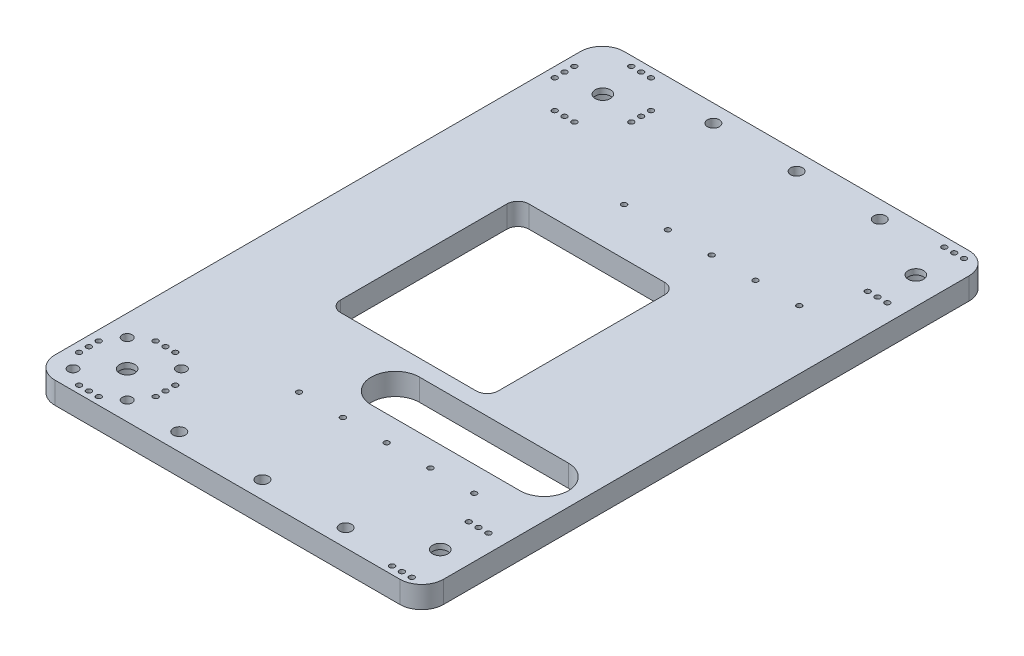
SolidWorks part; units mm, degrees
ref_plane "Front Plane" through (0, 0, 0) normal (0, 0, 1) x (1, 0, 0)
ref_plane "Top Plane" through (0, 0, 0) normal (0, 1, 0) x (1, 0, 0)
ref_plane "Right Plane" through (0, 0, 0) normal (1, 0, 0) x (0, 0, -1)
sketch "Sketch1" plane through (0, 0, 0) normal (0, 1, 0) x (1, 0, 0)
  line L0 (0, 134.94) -> (165, 134.94) construction
  line L1 (10, 0) -> (167.5, 0)
  line L2 (0, 10) -> (0, 250)
  line L3 (10, 260) -> (167.5, 260)
  line L4 (177.5, 10) -> (177.5, 250)
  line L7 (48.5, 91.94) -> (110.5, 91.94)
  line L8 (43.5, 96.94) -> (43.5, 172.94)
  line L9 (48.5, 177.94) -> (110.5, 177.94)
  line L10 (115.5, 96.94) -> (115.5, 172.94)
  line L11 (43.5, 91.94) -> (115.5, 177.94) construction
  line L12 (43.5, 177.94) -> (115.5, 91.94) construction
  arc A0 (0, 10) -> (10, 0) centre (10, 10) ccw
  arc A1 (167.5, 0) -> (177.5, 10) centre (167.5, 10) ccw
  arc A2 (177.5, 250) -> (167.5, 260) centre (167.5, 250) ccw
  arc A3 (10, 260) -> (0, 250) centre (10, 250) ccw
  arc A7 (110.5, 177.94) -> (115.5, 172.94) centre (110.5, 172.94) cw
  arc A8 (115.5, 96.94) -> (110.5, 91.94) centre (110.5, 96.94) cw
  arc A9 (48.5, 91.94) -> (43.5, 96.94) centre (48.5, 96.94) cw
  arc A11 (43.5, 172.94) -> (48.5, 177.94) centre (48.5, 172.94) cw
  point P7 (0, 0)
  point P10 (177.5, 0)
  point P15 (0, 260)
  point P20 (35, 60)
  point P21 (35, 190)
  point P28 (79.5, 134.94)
  point P29 (15.4848, 130)
  point P31 (135.4848, 130)
  point P44 (15.4848, 120)
  point P45 (135.4848, 120)
  dimension "D3" = 10
  dimension "D5" = 79.5
  dimension "D8" = 5
  dimension "D1" = 177.5
  dimension "D2" = 260
  dimension "D4" = 125.06
  dimension "D6" = 86
  dimension "D7" = 72
extrude "Boss-Extrude1" add sketch "Sketch1" along normal blind 10
sketch "Sketch3" plane through (0, 10, 0) normal (0, 1, 0) x (1, 0, 0)
  line L0 (92, 73.46) -> (160, 73.46) construction
  line L1 (92, 84.46) -> (92, 62.46) construction
  line L2 (92, 84.46) -> (160, 84.46)
  line L3 (160, 84.46) -> (160, 62.46) construction
  line L4 (43.5, 134.94) -> (115.5, 134.94) construction
  line L5 (92, 62.46) -> (160, 62.46)
  line L6 (43.5, 172.94) -> (43.5, 96.94) construction
  line L7 (115.5, 96.94) -> (115.5, 172.94) construction
  line L8 (177.5, 10) -> (177.5, 250) construction
  arc A0 (92, 84.46) -> (92, 62.46) centre (92, 73.46) ccw
  arc A1 (160, 62.46) -> (160, 84.46) centre (160, 73.46) ccw
  dimension "D2" = 17.5
  dimension "D4" = 68
  dimension "D1" = 61.48
  dimension "D3" = 22
extrude "Cut-Extrude2" cut sketch "Sketch3" against normal through all
sketch "Sketch5" plane through (0, 0, 0) normal (0, 1, 0) x (1, 0, 0)
  line L0 (0, 250) -> (0, 10) construction
  line L1 (10, 0) -> (167.5, 0) construction
  line L3 (22, 20.97) -> (165, 20.97) construction
  line L5 (22, 20.97) -> (22, 238.23) construction
  line L6 (22, 238.23) -> (165, 238.23) construction
  line L7 (165, 20.97) -> (165, 238.23) construction
  line L9 (177.5, 10) -> (177.5, 250) construction
  circle A0 centre (22, 20.97) radius 9.5
  circle A1 centre (165, 20.97) radius 9.5
  circle A2 centre (165, 238.23) radius 9.5
  circle A3 centre (22, 238.23) radius 9.5
  dimension "D1" = 12.5
  dimension "D2" = 22
  dimension "D5" = 19
  dimension "D4" = 20.97
  dimension "D3" = 217.26
extrude "Cut-Extrude4" cut sketch "Sketch5" along normal blind 6.5
sketch "Sketch7" plane through (0, 6.5, 0) normal (0, 1, 0) x (1, 0, 0)
  circle A0 centre (22, 20.97) radius 8
  circle A1 centre (165, 20.97) radius 8
  circle A2 centre (165, 238.23) radius 8
  circle A3 centre (22, 238.23) radius 8
  dimension "D1" = 16
extrude "Cut-Extrude5" cut sketch "Sketch7" along normal blind 1
sketch "Sketch8" plane through (0, 10, 0) normal (0, 1, 0) x (1, 0, 0)
  line L0 (22, 20.97) -> (165, 20.97) construction
  line L1 (165, 20.97) -> (165, 238.23) construction
  line L2 (93.5, 20.97) -> (93.5, 72.7554) construction
  line L3 (165, 129.6) -> (94.2743, 129.6) construction
  circle A0 centre (22, 20.97) radius 3.5
  circle A1 centre (165, 20.97) radius 3.5
  circle A2 centre (165, 238.23) radius 3.5
  circle A3 centre (22, 238.23) radius 3.5
  dimension "D1" = 7
extrude "Cut-Extrude6" cut sketch "Sketch8" against normal through all
hole_wizard "M4 Clearance Hole1" positions "Sketch11" profile "Sketch10" hole size "M4" standard "ISO" end condition through all
sketch "Sketch11" plane through (0, 10, 0) normal (0, 1, 0) x (-1, 0, 0)
  line L1 (-9.6256, -8.5956) -> (-34.3744, -8.5956) construction
  line L2 (-9.6256, -8.5956) -> (-9.6256, -33.3444) construction
  line L3 (-9.6256, -33.3444) -> (-34.3744, -33.3444) construction
  line L4 (-34.3744, -8.5956) -> (-34.3744, -33.3444) construction
  line L5 (-9.6256, -8.5956) -> (-34.3744, -33.3444) construction
  line L6 (-9.6256, -33.3444) -> (-34.3744, -8.5956) construction
  circle A0 centre (-22, -20.97) radius 17.5 construction
  circle A3 centre (-22, -20.97) radius 3.5 construction
  point P0 (-9.6256, -33.3444)
  point P1 (-34.3744, -33.3444)
  point P3 (-34.3744, -8.5956)
  point P5 (-9.6256, -8.5956)
  dimension "D1" = 35
sketch "Sketch10" plane through (9.6256, 10, -33.3444) normal (1, 0, 0) x (0, 0, 1)
  line L0 (0, 0) -> (0, 10)
  line L1 (0, 10) -> (2.25, 10)
  line L2 (2.25, 10) -> (2.25, 0)
  line L5 (2.25, 0) -> (0, 0)
  line L11 (0, -6.35) -> (0, 107.95) construction
  dimension "Thru Hole Dia." = 4.5
  dimension "Thru Hole Depth" = 10
hole_wizard "M2 Clearance Hole1" positions "Sketch14" profile "Sketch13" hole size "M2" standard "ISO" end condition through all
sketch "Sketch14" plane through (0, 10, 0) normal (0, 1, 0) x (-1, 0, 0)
  line L0 (-177.5, -50.96) -> (-50.3395, -50.96) construction
  line L1 (-177.5, -10) -> (-177.5, -250) construction
  line L8 (-70.5, -199.46) -> (-150.5, -199.46) construction
  line L9 (-115.5, -134.94) -> (-69.9149, -134.94) construction
  line L10 (-115.5, -96.94) -> (-115.5, -172.94) construction
  point P0 (-150.5, -50.96)
  point P17 (-130.5, -50.96)
  point P19 (-110.5, -50.96)
  point P21 (-90.5, -50.96)
  point P23 (-70.5, -50.96)
  point P48 (-70.5, -199.46)
  point P49 (-90.5, -199.46)
  point P50 (-110.5, -199.46)
  point P51 (-130.5, -199.46)
  point P52 (-150.5, -199.46)
  dimension "D1" = 83.98
  dimension "D2" = 27
  dimension "D3" = 20
  dimension "D4" = 20
  dimension "D5" = 20
  dimension "D6" = 20
  dimension "D7" = 64.52
sketch "Sketch13" plane through (150.5, 10, -50.96) normal (1, 0, 0) x (0, 0, 1)
  line L0 (0, 0) -> (0, 10)
  line L1 (0, 10) -> (1.2, 10)
  line L2 (1.2, 10) -> (1.2, 0)
  line L5 (1.2, 0) -> (0, 0)
  line L11 (0, -6.35) -> (0, 107.95) construction
  dimension "Thru Hole Dia." = 2.4
  dimension "Thru Hole Depth" = 10
hole_wizard "M2 Clearance Hole2" positions "Sketch16" profile "Sketch15" hole size "M2" standard "ISO" end condition through all
sketch "Sketch16" plane through (0, 10, 0) normal (0, 1, 0) x (-1, 0, 0)
  line L0 (-177.5, -3.47) -> (-129.2015, -3.47) construction
  line L1 (-177.5, -10) -> (-177.5, -250) construction
  line L3 (-10, 0) -> (-167.5, 0) construction
  line L4 (-165, -20.97) -> (-22, -20.97) construction
  line L6 (-93.5, -20.97) -> (-93.5, -14.0761) construction
  line L8 (-165, -20.97) -> (-165, -238.23) construction
  line L10 (-22, -20.97) -> (-22, -51.973) construction
  line L11 (-4.5, 0) -> (-4.5, -75.94) construction
  line L13 (0, -250) -> (0, -10) construction
  line L14 (-165, -129.6) -> (-68.1928, -129.6) construction
  line L15 (-22, -238.23) -> (-165, -238.23) construction
  line L17 (-22, -238.23) -> (-22, -20.97) construction
  circle A1 centre (-165, -20.97) radius 8 construction
  circle A2 centre (-22, -20.97) radius 3.5 construction
  circle A3 centre (-165, -238.23) radius 8 construction
  circle A4 centre (-22, -238.23) radius 3.5 construction
  point P0 (-165, -3.47)
  point P1 (-169.5, -3.47)
  point P14 (-160.5, -3.47)
  point P21 (-160.5, -38.47)
  point P22 (-169.5, -38.47)
  point P23 (-165, -38.47)
  point P79 (-165, -220.73)
  point P80 (-169.5, -220.73)
  point P81 (-160.5, -220.73)
  point P82 (-160.5, -255.73)
  point P83 (-169.5, -255.73)
  point P84 (-165, -255.73)
  point P87 (-39.5, -242.73)
  point P88 (-39.5, -233.73)
  point P89 (-39.5, -238.23)
  point P99 (-22, -255.73)
  point P100 (-17.5, -255.73)
  point P101 (-26.5, -255.73)
  point P102 (-26.5, -220.73)
  point P103 (-17.5, -220.73)
  point P104 (-22, -220.73)
  point P120 (-4.5, -238.23)
  point P121 (-4.5, -233.73)
  point P122 (-4.5, -242.73)
  dimension "D5" = 17.5
  dimension "D1" = 8
  dimension "D2" = 3.47
  dimension "D3" = 4.5
  dimension "D4" = 4.5
  dimension "D6" = 4.5
  dimension "D7" = 4.5
  dimension "D8" = 4.5
sketch "Sketch15" plane through (165, 10, -3.47) normal (1, 0, 0) x (0, 0, 1)
  line L0 (0, 0) -> (0, 10)
  line L1 (0, 10) -> (1.2, 10)
  line L2 (1.2, 10) -> (1.2, 0)
  line L5 (1.2, 0) -> (0, 0)
  line L11 (0, -6.35) -> (0, 107.95) construction
  dimension "Thru Hole Dia." = 2.4
  dimension "Thru Hole Depth" = 10
hole_wizard "CSK for M2 Countersunk Flat Head Screw1" positions "Sketch20" profile "Sketch19" countersink size "M2" standard "ISO" end condition through all
sketch "Sketch20" plane through (0, 0, 0) normal (0, -1, 0) x (1, 0, 0)
  line L5 (169.5, -3.47) -> (0, -3.47) construction
  line L7 (0, -250) -> (0, -10) construction
  line L8 (26.5, -255.73) -> (26.5, 0) construction
  line L9 (10, 0) -> (167.5, 0) construction
  line L12 (17.5, -255.73) -> (17.5, 0) construction
  line L14 (39.5, -242.73) -> (39.5, 0) construction
  line L16 (22, -20.97) -> (31.5, -20.97) construction
  line L18 (22, -20.97) -> (22, -11.47) construction
  circle A1 centre (22, -20.97) radius 9.5 construction
  circle A2 centre (22, -20.97) radius 9.5 construction
  point P0 (17.5, -3.47)
  point P1 (22, -3.47)
  point P3 (26.5, -3.47)
  point P5 (39.5, -16.47)
  point P7 (39.5, -20.97)
  point P9 (39.5, -25.47)
  point P77 (4.5, -25.47)
  point P78 (4.5, -20.97)
  point P79 (4.5, -16.47)
  point P80 (26.5, -38.47)
  point P81 (22, -38.47)
  point P82 (17.5, -38.47)
  dimension "D1" = 4.5
  dimension "D2" = 4.5
  dimension "D3" = 4.5
sketch "Sketch19" plane through (17.5, 0, -3.47) normal (1, 0, 0) x (0, 0, -1)
  line L0 (0, 0) -> (0, 10)
  line L1 (0, 10) -> (1.2, 10)
  line L2 (1.2, 10) -> (1.2, 1)
  line L3 (1.2, 1) -> (2.2, 0)
  line L5 (2.2, 0) -> (0, 0)
  line L6 (-1.2, 1) -> (-2.2, 0) construction
  line L11 (0, -6.35) -> (0, 107.95) construction
  dimension "Thru Hole Dia." = 2.4
  dimension "Thru Hole Depth" = 10
  dimension "Near C'Sink Dia." = 4.4
  dimension "Near C'Sink Angle" = 90
hole_wizard "M5 Clearance Hole1" positions "Sketch23" profile "Sketch22" hole size "M5" standard "ISO" end condition through all
sketch "Sketch23" plane through (0, 10, 0) normal (0, 1, 0) x (-1, 0, 0)
  line L0 (-10, 0) -> (-167.5, 0) construction
  line L1 (0, -250) -> (0, -10) construction
  line L2 (-177.5, -130) -> (0, -130) construction
  line L3 (-177.5, -10) -> (-177.5, -250) construction
  point P0 (-58.75, -8)
  point P1 (-96.75, -8)
  point P3 (-134.75, -8)
  point P22 (-134.75, -252)
  point P23 (-96.75, -252)
  point P24 (-58.75, -252)
  dimension "D1" = 8
  dimension "D2" = 58.75
  dimension "D3" = 38
  dimension "D4" = 38
sketch "Sketch22" plane through (58.75, 10, -8) normal (1, 0, 0) x (0, 0, 1)
  line L0 (0, 0) -> (0, 10)
  line L1 (0, 10) -> (2.75, 10)
  line L2 (2.75, 10) -> (2.75, 0)
  line L5 (2.75, 0) -> (0, 0)
  line L11 (0, -6.35) -> (0, 107.95) construction
  dimension "Thru Hole Dia." = 5.5
  dimension "Thru Hole Depth" = 10
equation "\"D4@Sketch14\" = \"D3@Sketch14\""
equation "\"D5@Sketch14\" = \"D3@Sketch14\""
equation "\"D6@Sketch14\" = \"D3@Sketch14\""
equation "\"D4@Sketch16\" = \"D3@Sketch16\""
equation "\"D6@Sketch16\" = \"D3@Sketch16\""
equation "\"D8@Sketch16\" = \"D6@Sketch16\""
equation "\"D2@Sketch20\" = \"D1@Sketch20\""
equation "\"D3@Sketch20\" = \"D2@Sketch20\""
equation "\"D4@Sketch23\" = \"D3@Sketch23\""
